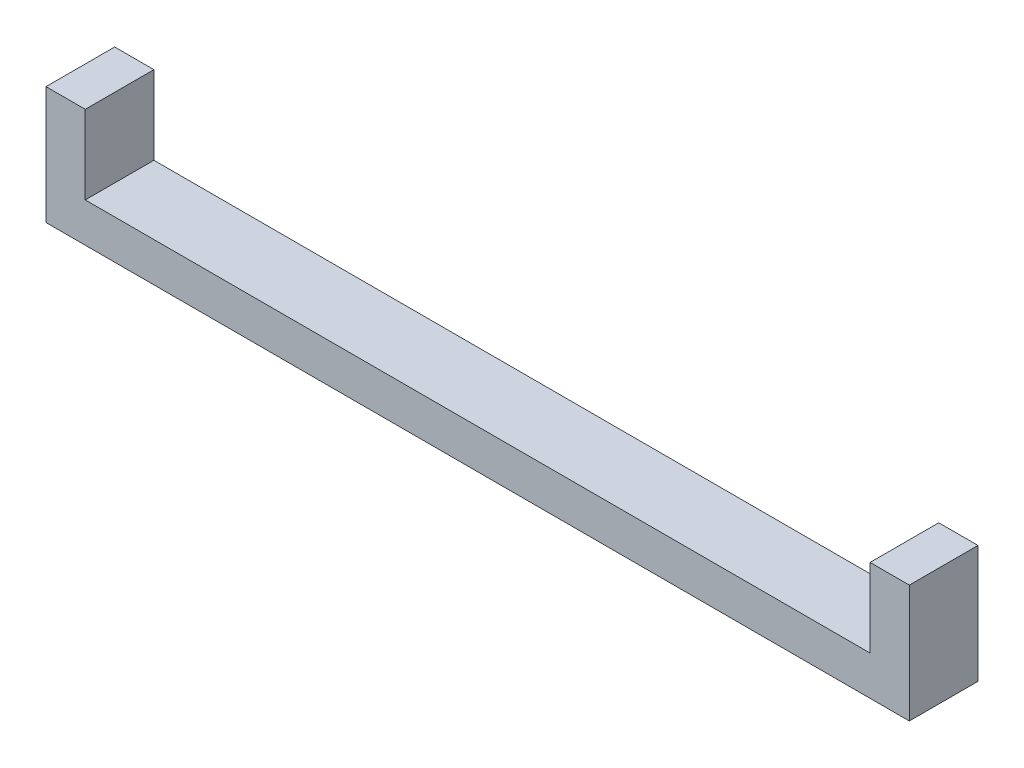
SolidWorks part; units mm, degrees
ref_plane "Front Plane" through (0, 0, 0) normal (0, 0, 1) x (1, 0, 0)
ref_plane "Top Plane" through (0, 0, 0) normal (0, 1, 0) x (1, 0, 0)
ref_plane "Right Plane" through (0, 0, 0) normal (1, 0, 0) x (0, 0, -1)
sketch "Sketch1" plane through (0, 0, 0) normal (0, 0, 1) x (1, 0, 0)
  line L0 (0, 0) -> (200, 0)
  line L1 (200, 0) -> (200, 40)
  line L2 (0, 0) -> (0, 37.0161) construction
  dimension "D1" = 40
  dimension "D2" = 400
extrude "Extrude-Thin1" add sketch "Sketch1" along normal mid plane 35.001 thin
mirror "Mirror1" about plane through (0, 0, 0) normal (1, 0, 0) of "Extrude-Thin1"
